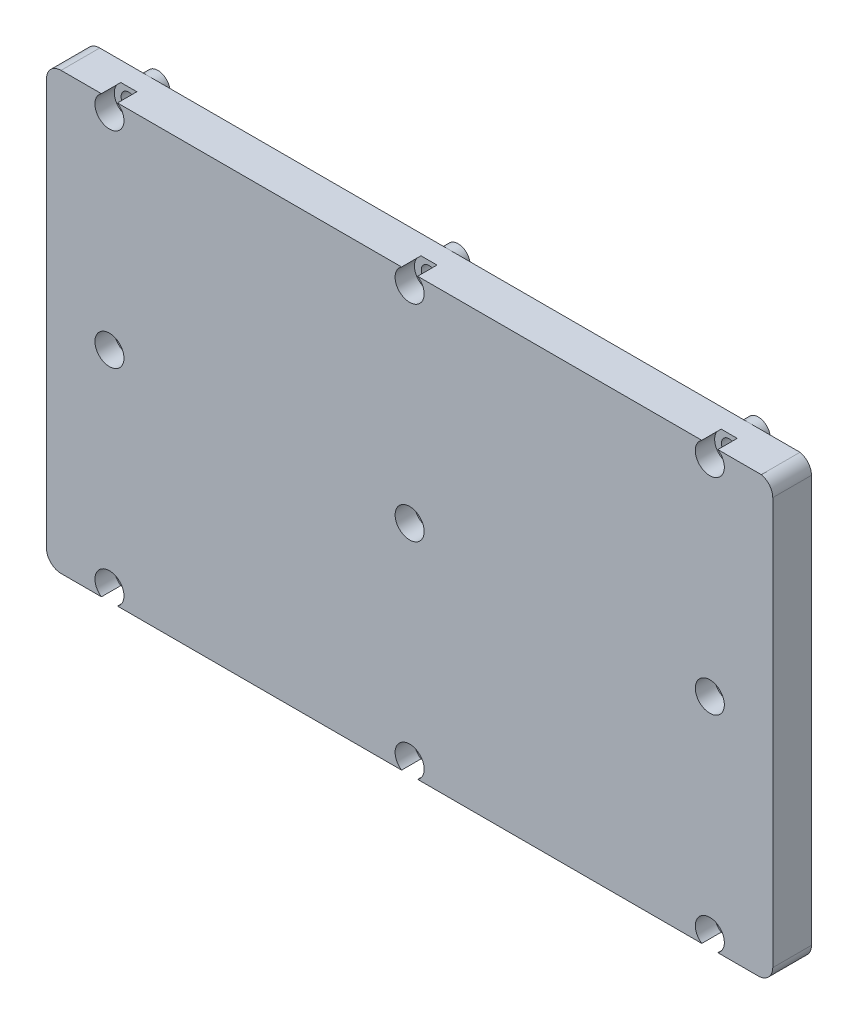
SolidWorks part; units mm, degrees
ref_plane "Plan de face" through (0, 0, 0) normal (0, 0, 1) x (1, 0, 0)
ref_plane "Plan de dessus" through (0, 0, 0) normal (0, 1, 0) x (1, 0, 0)
ref_plane "Plan de droite" through (0, 0, 0) normal (1, 0, 0) x (0, 0, -1)
sketch "Esquisse1" plane through (0, 0, 0) normal (0, 0, 1) x (1, 0, 0)
  line L5 (2.9684, 10.0302) -> (146.9684, 10.0302)
  line L6 (-0.0316, 13.0302) -> (-0.0316, 97.0302)
  line L7 (149.9684, 13.0302) -> (149.9684, 97.0969)
  line L10 (2.9684, 100.0302) -> (147.5976, 100.0302)
  arc A0 (2.9684, 10.0302) -> (-0.0316, 13.0302) centre (2.9684, 13.0302) cw
  arc A1 (146.9684, 10.0302) -> (149.9684, 13.0302) centre (146.9684, 13.0302) ccw
  arc A2 (147.5976, 100.0302) -> (149.9684, 97.0969) centre (146.9684, 97.0969) cw
  arc A3 (-0.0316, 97.0302) -> (2.9684, 100.0302) centre (2.9684, 97.0302) cw
  point P17 (-0.0316, 100.0302)
  dimension "D1" = 3
  dimension "D18" = 150
  dimension "D19" = 90
extrude "Boss.-Extru.1" add sketch "Esquisse1" along normal blind 8
sketch "Esquisse14" plane through (0, 0, 8) normal (0, 0, 1) x (1, 0, 0)
  line L0 (-0.0316, 97.0302) -> (-0.0316, 13.0302) construction
  line L1 (2.9684, 10.0302) -> (146.9684, 10.0302) construction
  circle A0 centre (12.9684, 97.5302) radius 1.6
  circle A1 centre (74.9684, 97.5302) radius 1.6
  circle A2 centre (136.9684, 97.5302) radius 1.6
  circle A3 centre (136.9684, 55.0302) radius 1.6
  circle A4 centre (74.9684, 55.0302) radius 1.6
  circle A5 centre (12.9684, 55.0302) radius 1.6
  circle A6 centre (12.9684, 12.5302) radius 1.6
  circle A7 centre (74.9684, 12.5302) radius 1.6
  circle A8 centre (136.9684, 12.5302) radius 1.6
  dimension "D1" = 13
  dimension "D2" = 13
  dimension "D3" = 13
  dimension "D4" = 62
  dimension "D5" = 62
  dimension "D6" = 62
  dimension "D7" = 42.5
  dimension "D8" = 42.5
  dimension "D9" = 2.5
  dimension "D10" = 2.5
  dimension "D11" = 2.5
  dimension "D12" = 42.5
  dimension "D13" = 42.5
  dimension "D14" = 62
  dimension "D15" = 62
  dimension "D16" = 62
  dimension "D17" = 42.5
  dimension "D18" = 42.5
extrude "Enlèv. mat.-Extru.2" cut sketch "Esquisse14" against normal through all both and the other way through all
sketch "Esquisse15" plane through (0, 0, 8) normal (0, 0, 1) x (1, 0, 0)
  circle A0 centre (12.9684, 97.5302) radius 3
  circle A1 centre (12.9684, 12.5302) radius 3
  circle A2 centre (74.9684, 12.5302) radius 3
  circle A3 centre (136.9684, 12.5302) radius 3
  circle A4 centre (136.9684, 55.0302) radius 3
  circle A5 centre (74.9684, 55.0302) radius 3
  circle A6 centre (12.9684, 55.0302) radius 3
  circle A7 centre (74.9684, 97.5302) radius 3
  circle A8 centre (136.9684, 97.5302) radius 3
extrude "Enlèv. mat.-Extru.3" cut sketch "Esquisse15" against normal blind 4
sketch "Esquisse16" plane through (0, 0, 0) normal (0, 0, -1) x (-1, 0, 0)
  circle A0 centre (-136.9684, 97.5302) radius 2.5
  circle A1 centre (-74.9684, 97.5302) radius 2.5
  circle A2 centre (-12.9684, 97.5302) radius 2.5
  circle A3 centre (-12.9684, 55.0302) radius 2.5
  circle A4 centre (-74.9684, 55.0302) radius 2.5
  circle A5 centre (-136.9684, 55.0302) radius 2.5
  circle A6 centre (-136.9684, 12.5302) radius 2.5
  circle A7 centre (-74.9684, 12.5302) radius 2.5
  circle A8 centre (-12.9684, 12.5302) radius 2.5
extrude "Boss.-Extru.3" add sketch "Esquisse16" along normal blind 2
sketch "Esquisse17" plane through (0, 0, -2) normal (0, 0, -1) x (-1, 0, 0)
  circle A0 centre (-136.9684, 97.5302) radius 1.6
  circle A1 centre (-136.9684, 55.0302) radius 1.6
  circle A2 centre (-136.9684, 12.5302) radius 1.6
  circle A3 centre (-74.9684, 12.5302) radius 1.6
  circle A4 centre (-74.9684, 55.0302) radius 1.6
  circle A5 centre (-74.9684, 97.5302) radius 1.6
  circle A6 centre (-12.9684, 97.5302) radius 1.6
  circle A7 centre (-12.9684, 55.0302) radius 1.6
  circle A8 centre (-12.9684, 12.5302) radius 1.6
extrude "Enlèv. mat.-Extru.4" cut sketch "Esquisse17" against normal through all
